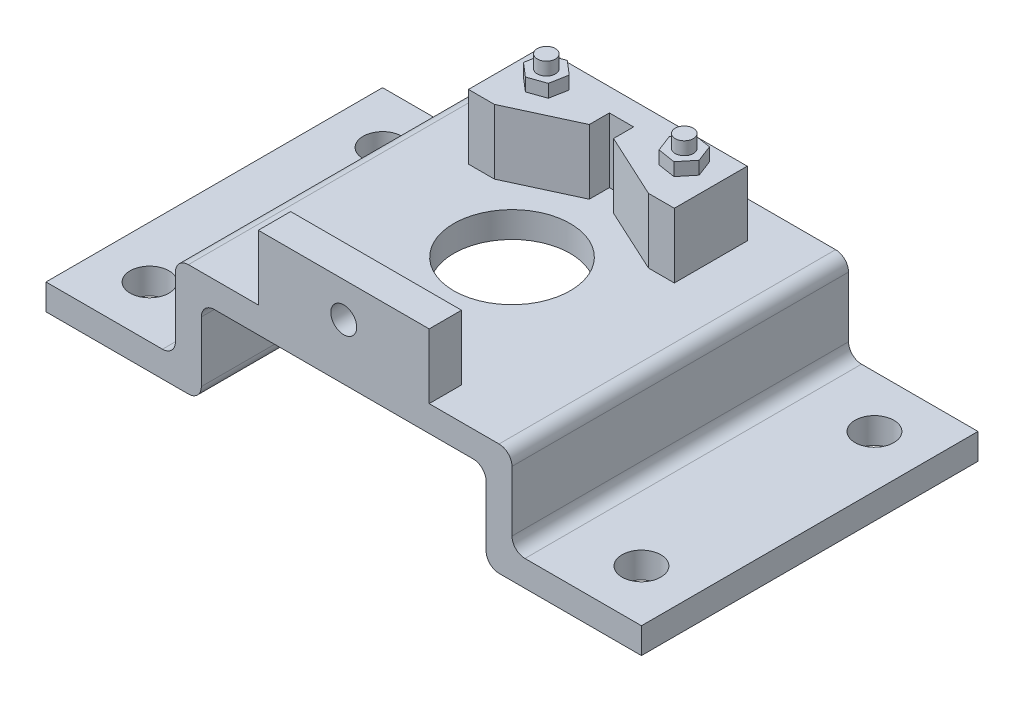
SolidWorks part; units mm, degrees
ref_plane "前视基准面" through (0, 0, 0) normal (0, 0, 1) x (1, 0, 0)
ref_plane "上视基准面" through (0, 0, 0) normal (0, 1, 0) x (1, 0, 0)
ref_plane "右视基准面" through (0, 0, 0) normal (1, 0, 0) x (0, 0, -1)
sketch "草图1" plane through (0, 0, 0) normal (0, 0, 1) x (1, 0, 0)
  line L0 (0, 26.763) -> (0, -88.9106)
  line L1 (-110, 0) -> (110, 0)
  line L2 (-230, -66.599) -> (-230, -46.599)
  line L3 (-130, 20) -> (130, 20)
  line L4 (130, 10.8395) -> (130, 20)
  line L5 (-109.6704, -66.599) -> (-230, -66.599)
  line L6 (110, 0) -> (110, -66.599)
  line L7 (110, -66.599) -> (109.6704, -66.599)
  line L8 (130, 10.8395) -> (130, -46.599)
  line L9 (109.6704, -66.599) -> (230, -66.599)
  line L10 (-130, -46.599) -> (-230, -46.599)
  line L11 (130, -46.599) -> (230, -46.599)
  line L12 (230, -66.599) -> (230, -46.599)
  line L13 (-110, 0) -> (-110, -66.599)
  line L14 (-130, 10.8395) -> (-130, 20)
  line L15 (-130, 10.8395) -> (-130, -46.599)
  point P15 (0, 20)
  point P21 (0, 0)
  dimension "D1" = 130
  dimension "D2" = 20
  dimension "D3" = 20
  dimension "D4" = 20
  dimension "D5" = 100
extrude "凸台-拉伸1" add sketch "草图1" along normal mid plane 260 contours L14 L15 L10 L2 L5 L13 L1 L0 L3 | L9 L12 L11 L8 L4 L3 L0 L1 L6
fillet "圆角1" radius 10 8 edges at (110, -66.599, 0) (130, -46.599, 0) (130, 20, 0) (110, 0, 0) (-110, 0, 0) (-110, -66.599, 0) (-130, 20, 0) (-130, -46.599, 0)
sketch "草图2" plane through (0, 20, 0) normal (0, 1, 0) x (1, 0, 0)
  circle A0 centre (0, 0) radius 45
extrude "切除-拉伸1" cut sketch "草图2" against normal blind 260
sketch "草图3" plane through (0, 20, 0) normal (0, 1, 0) x (1, 0, 0)
  line L0 (-59.0456, 45.4122) -> (-8.888, 68.6042)
  line L1 (9.8395, 68.6042) -> (9.8395, 84.0973)
  line L2 (-59.0456, 45.4122) -> (-79.0456, 45.4122)
  line L3 (-79.0456, 45.4122) -> (-79.0456, 101.745)
  line L4 (-79.0456, 101.745) -> (79.997, 101.745)
  line L5 (59.997, 45.4122) -> (9.8395, 68.6042)
  line L6 (59.997, 45.4122) -> (79.997, 45.4122)
  line L7 (-8.888, 68.6042) -> (-8.888, 84.0973)
  line L8 (-8.888, 84.0973) -> (9.8395, 84.0973)
  line L9 (79.997, 45.4122) -> (79.997, 101.745)
  line L10 (0.4757, 84.0973) -> (0.4757, 101.745)
  circle A0 centre (0, 0) radius 66
  circle A1 centre (-52.7931, 79.333) radius 7
  circle A2 centre (53.7445, 79.333) radius 7
  dimension "D1" = 132.0001
  dimension "D2" = 20
extrude "凸台-拉伸2" add sketch "草图3" along normal blind 50 contours L10 L8 L1 L5 L6 L9 L4 A2 | L8 L10 L4 L3 L2 L0 L7 A1
sketch "草图4" plane through (0, 70, 0) normal (0, 1, 0) x (1, 0, 0)
  line L1 (48.7956, 92.2756) -> (40.0615, 81.5184)
  line L2 (40.0615, 81.5184) -> (45.0104, 68.5759)
  line L3 (45.0104, 68.5759) -> (58.6934, 66.3905)
  line L4 (58.6934, 66.3905) -> (67.4275, 77.1476)
  line L5 (67.4275, 77.1476) -> (62.4786, 90.0901)
  line L6 (62.4786, 90.0901) -> (48.7956, 92.2756)
  line L7 (-50.2279, 92.9499) -> (-63.3031, 88.363)
  line L8 (-63.3031, 88.363) -> (-65.8682, 74.7461)
  line L9 (-65.8682, 74.7461) -> (-55.3582, 65.7161)
  line L10 (-55.3582, 65.7161) -> (-42.2831, 70.3031)
  line L11 (-42.2831, 70.3031) -> (-39.7179, 83.92)
  line L12 (-39.7179, 83.92) -> (-50.2279, 92.9499)
  circle A0 centre (53.7445, 79.333) radius 7
  circle A1 centre (53.7445, 79.333) radius 12 construction
  circle A2 centre (-52.7931, 79.333) radius 12 construction
  circle A3 centre (-52.7931, 79.333) radius 7
extrude "凸台-拉伸3" add sketch "草图4" along normal blind 10
sketch "草图5" plane through (0, 20, 0) normal (0, 1, 0) x (1, 0, 0)
  circle A1 centre (53.7445, 79.333) radius 7
  circle A2 centre (-52.7931, 79.333) radius 7
extrude "凸台-拉伸4" add sketch "草图5" along normal blind 70
sketch "草图6" plane through (0, 20, 0) normal (0, 1, 0) x (1, 0, 0)
  line L0 (-120, -130) -> (120, -130) construction
  line L1 (66, -130) -> (-66, -130)
  line L2 (66, -130) -> (66, -105)
  line L3 (66, -105) -> (-66, -105)
  line L4 (-66, -130) -> (-66, -105)
  dimension "D1" = 25
extrude "凸台-拉伸5" add sketch "草图6" along normal blind 50
sketch "草图7" plane through (0, 0, 130) normal (0, 0, 1) x (1, 0, 0)
  circle A0 centre (0, 43.0803) radius 10
extrude "切除-拉伸2" cut sketch "草图7" against normal blind 50
sketch "草图8" plane through (0, -46.599, 0) normal (0, 1, 0) x (1, 0, 0)
  line L0 (230, -130) -> (230, 130) construction
  line L1 (140, -130) -> (230, -130) construction
  line L2 (140, 130) -> (230, 130) construction
  line L3 (0, -224.7246) -> (0, 302.6619)
  circle A0 centre (190, 90) radius 15
  circle A1 centre (190, -90) radius 15
  circle A2 centre (-190, -90) radius 15
  circle A3 centre (-190, 90) radius 15
  dimension "D5" = 30
  dimension "D6" = 30
  dimension "D1" = 40
  dimension "D2" = 40
  dimension "D3" = 40
  dimension "D4" = 40
extrude "切除-拉伸3" cut sketch "草图8" against normal blind 30 contours A2 | A3 | A0 | A1
